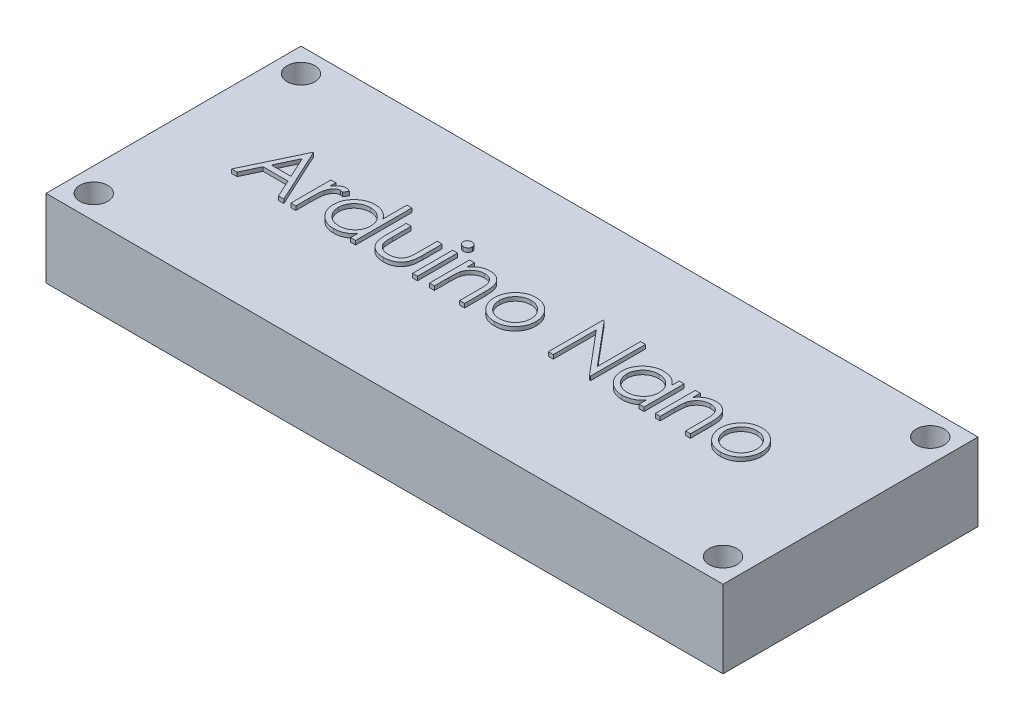
SolidWorks part; units mm, degrees
ref_plane "Front Plane" through (0, 0, 0) normal (0, 0, 1) x (1, 0, 0)
ref_plane "Top Plane" through (0, 0, 0) normal (0, 1, 0) x (1, 0, 0)
ref_plane "Right Plane" through (0, 0, 0) normal (1, 0, 0) x (0, 0, -1)
sketch "Sketch1" plane through (0, 0, 0) normal (0, 1, 0) x (1, 0, 0)
  line L0 (0, 0) -> (-21.59, 0) construction
  line L1 (-21.59, 8.1321) -> (21.59, 8.1321)
  line L2 (-21.59, 8.1321) -> (-21.59, -8.1321)
  line L3 (-21.59, -8.1321) -> (21.59, -8.1321)
  line L4 (21.59, 8.1321) -> (21.59, -8.1321)
  line L5 (-21.59, 8.1321) -> (21.59, -8.1321) construction
  line L6 (-21.59, -8.1321) -> (21.59, 8.1321) construction
  line L7 (-21.59, 0) -> (21.59, 0) construction
  circle A0 centre (-20.066, 6.6081) radius 0.889
  circle A1 centre (20.066, 6.6081) radius 0.889
  circle A4 centre (20.066, -6.6081) radius 0.889
  circle A5 centre (-20.066, -6.6081) radius 0.889
  point P0 (0, 0)
  dimension "D2" = 1.778
  dimension "D7" = 1.524
  dimension "D1" = 43.18
  dimension "D3" = 1.524
  dimension "D4" = 1.524
  dimension "D5" = 2
  dimension "D6" = 1
extrude "Boss-Extrude1" add sketch "Sketch1" against normal blind 4.953
sketch "Sketch2" plane through (0, 0, 0) normal (0, 1, 0) x (1, 0, 0)
  text T0 "Arduino Nano"
extrude "Boss-Extrude2" add sketch "Sketch2" along normal blind 0.254
